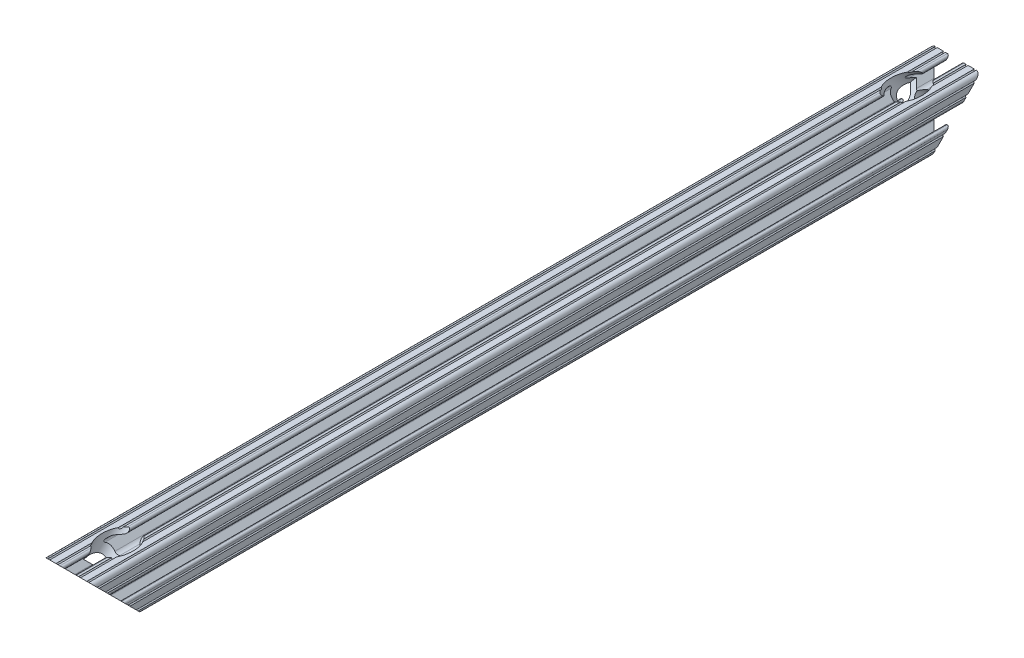
SolidWorks part; units mm, degrees
ref_plane "Front Plane" through (0, 0, 0) normal (0, 0, 1) x (1, 0, 0)
ref_plane "Top Plane" through (0, 0, 0) normal (0, 1, 0) x (1, 0, 0)
ref_plane "Right Plane" through (0, 0, 0) normal (1, 0, 0) x (0, 0, -1)
sketch "Sketch1" plane through (0, 0, 0) normal (0, 0, 1) x (1, 0, 0)
  line L2 (-7.1797, -8.6452) -> (-3.9523, -5.4237)
  line L3 (-1.7093, -4.4958) -> (1.7093, -4.4958)
  line L4 (3.9523, -5.4237) -> (7.1797, -8.6452)
  line L6 (6.4164, -10.4902) -> (4.2875, -10.4902)
  line L7 (3.2385, -11.5392) -> (3.2385, -11.651)
  line L8 (4.2875, -12.7) -> (5.3171, -12.7)
  line L9 (6.3331, -12.7) -> (9.5504, -12.7)
  line L10 (12.7, -9.5504) -> (12.7, -6.3331)
  line L11 (12.7, -5.3171) -> (12.7, -4.2875)
  line L12 (11.651, -3.2385) -> (11.5392, -3.2385)
  line L13 (10.4902, -4.2875) -> (10.4902, -6.4021)
  line L14 (8.7371, -7.1294) -> (5.441, -3.8408)
  line L15 (4.5085, -1.5932) -> (4.5085, 1.5932)
  line L16 (5.441, 3.8408) -> (8.7371, 7.1294)
  line L17 (10.4902, 6.4021) -> (10.4902, 4.2875)
  line L18 (11.5392, 3.2385) -> (11.651, 3.2385)
  line L19 (12.7, 4.2875) -> (12.7, 5.3171)
  line L20 (12.7, 6.3331) -> (12.7, 9.5504)
  line L21 (9.5504, 12.7) -> (6.3331, 12.7)
  line L22 (5.3171, 12.7) -> (4.2875, 12.7)
  line L23 (3.2385, 11.651) -> (3.2385, 11.5392)
  line L24 (4.2875, 10.4902) -> (6.4768, 10.4902)
  line L25 (7.207, 8.7244) -> (3.8983, 5.4232)
  line L26 (1.6558, 4.4958) -> (-1.6558, 4.4958)
  line L27 (-3.8983, 5.4232) -> (-7.207, 8.7244)
  line L28 (-6.4768, 10.4902) -> (-4.2875, 10.4902)
  line L29 (-3.2385, 11.5392) -> (-3.2385, 11.651)
  line L30 (-4.2875, 12.7) -> (-5.3171, 12.7)
  line L31 (-6.3331, 12.7) -> (-9.5504, 12.7)
  line L32 (-12.7, 9.5504) -> (-12.7, 6.3331)
  line L33 (-12.7, 5.3171) -> (-12.7, 4.2875)
  line L34 (-11.651, 3.2385) -> (-11.5392, 3.2385)
  line L35 (-10.4902, 4.2875) -> (-10.4902, 6.4021)
  line L36 (-8.7371, 7.1294) -> (-5.441, 3.8408)
  line L37 (-4.5085, 1.5932) -> (-4.5085, -1.5932)
  line L38 (-5.441, -3.8408) -> (-8.7371, -7.1294)
  line L39 (-10.4902, -6.4021) -> (-10.4902, -4.2875)
  line L40 (-11.5392, -3.2385) -> (-11.651, -3.2385)
  line L41 (-12.7, -4.2875) -> (-12.7, -5.3171)
  line L42 (-12.7, -6.3331) -> (-12.7, -9.5504)
  line L43 (-9.5504, -12.7) -> (-6.3331, -12.7)
  line L44 (-5.3171, -12.7) -> (-4.2875, -12.7)
  line L45 (-3.2385, -11.651) -> (-3.2385, -11.5392)
  line L46 (-4.2875, -10.4902) -> (-6.4164, -10.4902)
  circle A0 centre (0, 0) radius 2.6035
  arc A1 (-7.1797, -8.6452) -> (-6.4164, -10.4902) centre (-6.4164, -9.4098) ccw
  arc A2 (-1.7093, -4.4958) -> (-3.9523, -5.4237) centre (-1.7093, -7.6708) ccw
  arc A3 (3.9523, -5.4237) -> (1.7093, -4.4958) centre (1.7093, -7.6708) ccw
  arc A4 (6.4164, -10.4902) -> (7.1797, -8.6452) centre (6.4164, -9.4098) ccw
  arc A5 (4.2875, -10.4902) -> (3.2385, -11.5392) centre (4.2875, -11.5392) ccw
  arc A6 (3.2385, -11.651) -> (4.2875, -12.7) centre (4.2875, -11.651) ccw
  arc A7 (6.3331, -12.7) -> (5.3171, -12.7) centre (5.8251, -12.7) ccw
  arc A8 (10.5664, -12.6998) -> (9.5504, -12.7) centre (10.0584, -12.7) ccw
  arc A9 (10.5664, -12.6998) -> (12.6998, -10.5664) centre (10.5918, -10.5918) ccw
  arc A10 (12.7, -9.5504) -> (12.6998, -10.5664) centre (12.7, -10.0584) ccw
  arc A11 (12.7, -5.3171) -> (12.7, -6.3331) centre (12.7, -5.8251) ccw
  arc A12 (12.7, -4.2875) -> (11.651, -3.2385) centre (11.651, -4.2875) ccw
  arc A13 (11.5392, -3.2385) -> (10.4902, -4.2875) centre (11.5392, -4.2875) ccw
  arc A14 (8.7371, -7.1294) -> (10.4902, -6.4021) centre (9.4628, -6.4021) ccw
  arc A15 (4.5085, -1.5932) -> (5.441, -3.8408) centre (7.6835, -1.5932) ccw
  arc A16 (5.441, 3.8408) -> (4.5085, 1.5932) centre (7.6835, 1.5932) ccw
  arc A17 (10.4902, 6.4021) -> (8.7371, 7.1294) centre (9.4628, 6.4021) ccw
  arc A18 (10.4902, 4.2875) -> (11.5392, 3.2385) centre (11.5392, 4.2875) ccw
  arc A19 (11.651, 3.2385) -> (12.7, 4.2875) centre (11.651, 4.2875) ccw
  arc A20 (12.7, 6.3331) -> (12.7, 5.3171) centre (12.7, 5.8251) ccw
  arc A21 (12.6998, 10.5664) -> (12.7, 9.5504) centre (12.7, 10.0584) ccw
  arc A22 (12.6998, 10.5664) -> (10.5664, 12.6998) centre (10.5918, 10.5918) ccw
  arc A23 (9.5504, 12.7) -> (10.5664, 12.6998) centre (10.0584, 12.7) ccw
  arc A24 (5.3171, 12.7) -> (6.3331, 12.7) centre (5.8251, 12.7) ccw
  arc A25 (4.2875, 12.7) -> (3.2385, 11.651) centre (4.2875, 11.651) ccw
  arc A26 (3.2385, 11.5392) -> (4.2875, 10.4902) centre (4.2875, 11.5392) ccw
  arc A27 (7.207, 8.7244) -> (6.4768, 10.4902) centre (6.4768, 9.4563) ccw
  arc A28 (1.6558, 4.4958) -> (3.8983, 5.4232) centre (1.6558, 7.6708) ccw
  arc A29 (-3.8983, 5.4232) -> (-1.6558, 4.4958) centre (-1.6558, 7.6708) ccw
  arc A30 (-6.4768, 10.4902) -> (-7.207, 8.7244) centre (-6.4768, 9.4563) ccw
  arc A31 (-4.2875, 10.4902) -> (-3.2385, 11.5392) centre (-4.2875, 11.5392) ccw
  arc A32 (-3.2385, 11.651) -> (-4.2875, 12.7) centre (-4.2875, 11.651) ccw
  arc A33 (-6.3331, 12.7) -> (-5.3171, 12.7) centre (-5.8251, 12.7) ccw
  arc A34 (-10.5664, 12.6998) -> (-9.5504, 12.7) centre (-10.0584, 12.7) ccw
  arc A35 (-10.5664, 12.6998) -> (-12.6998, 10.5664) centre (-10.5918, 10.5918) ccw
  arc A36 (-12.7, 9.5504) -> (-12.6998, 10.5664) centre (-12.7, 10.0584) ccw
  arc A37 (-12.7, 5.3171) -> (-12.7, 6.3331) centre (-12.7, 5.8251) ccw
  arc A38 (-12.7, 4.2875) -> (-11.651, 3.2385) centre (-11.651, 4.2875) ccw
  arc A39 (-11.5392, 3.2385) -> (-10.4902, 4.2875) centre (-11.5392, 4.2875) ccw
  arc A40 (-8.7371, 7.1294) -> (-10.4902, 6.4021) centre (-9.4628, 6.4021) ccw
  arc A41 (-4.5085, 1.5932) -> (-5.441, 3.8408) centre (-7.6835, 1.5932) ccw
  arc A42 (-5.441, -3.8408) -> (-4.5085, -1.5932) centre (-7.6835, -1.5932) ccw
  arc A43 (-10.4902, -6.4021) -> (-8.7371, -7.1294) centre (-9.4628, -6.4021) ccw
  arc A44 (-10.4902, -4.2875) -> (-11.5392, -3.2385) centre (-11.5392, -4.2875) ccw
  arc A45 (-11.651, -3.2385) -> (-12.7, -4.2875) centre (-11.651, -4.2875) ccw
  arc A46 (-12.7, -6.3331) -> (-12.7, -5.3171) centre (-12.7, -5.8251) ccw
  arc A47 (-12.6998, -10.5664) -> (-12.7, -9.5504) centre (-12.7, -10.0584) ccw
  arc A48 (-12.6998, -10.5664) -> (-10.5664, -12.6998) centre (-10.5918, -10.5918) ccw
  arc A49 (-9.5504, -12.7) -> (-10.5664, -12.6998) centre (-10.0584, -12.7) ccw
  arc A50 (-5.3171, -12.7) -> (-6.3331, -12.7) centre (-5.8251, -12.7) ccw
  arc A51 (-4.2875, -12.7) -> (-3.2385, -11.651) centre (-4.2875, -11.651) ccw
  arc A52 (-3.2385, -11.5392) -> (-4.2875, -10.4902) centre (-4.2875, -11.5392) ccw
extrude "Boss-Extrude1" add sketch "Sketch1" along normal mid plane 457.2
sketch "Sketch2" plane through (0, 0, 0) normal (1, 0, 0) x (0, 0, -1)
  line L0 (-228.6, 12.6998) -> (-228.6, -12.7)
  line L1 (-228.6, -12.7) -> (-203.2002, -12.7)
  line L2 (-203.2002, -12.7) -> (-228.6, 12.6998)
  line L3 (0, 0) -> (0, -12.7) construction
  line L5 (203.2002, -12.7) -> (228.6, 12.6998)
  line L6 (228.6, -12.7) -> (203.2002, -12.7)
  line L7 (228.6, 12.6998) -> (228.6, -12.7)
  line L8 (-228.6, -12.7) -> (228.6, -12.7) construction
extrude "Cut-Extrude1" cut sketch "Sketch2" against normal through all and the other way through all
sketch "Sketch3" plane through (0, 0, 0) normal (1, 0, 0) x (0, 0, -1)
  line L0 (-197.5876, 18.3125) -> (-215.9002, 0)
  line L1 (-215.9002, 0) -> (-218.2081, 2.3079)
  line L2 (-218.2081, 2.3079) -> (-213.718, 6.7981)
  line L3 (-213.718, 6.7981) -> (-217.0227, 10.1028)
  line L4 (-217.0227, 10.1028) -> (-203.2003, 23.9252)
  line L5 (-203.2003, 23.9252) -> (-197.5876, 18.3125)
  line L6 (-215.9002, 0) -> (-218.2081, -2.3079) construction
  line L7 (-203.2002, -12.7) -> (-228.6, 12.6998) construction
  line L8 (-218.5037, 2.6035) -> (-213.2967, -2.6035) construction
  line L9 (-205.7974, -1.1225) -> (-191.975, 12.6998) construction
  dimension "D1" = 6.5278
  dimension "D2" = 15.875
  dimension "D3" = 6.35
revolve "Cut-Revolve1" cut sketch "Sketch3" angle 360 mid plane about L6
mirror "Mirror1" about plane through (0, 0, 0) normal (0, 0, 1) of "Cut-Revolve1"
